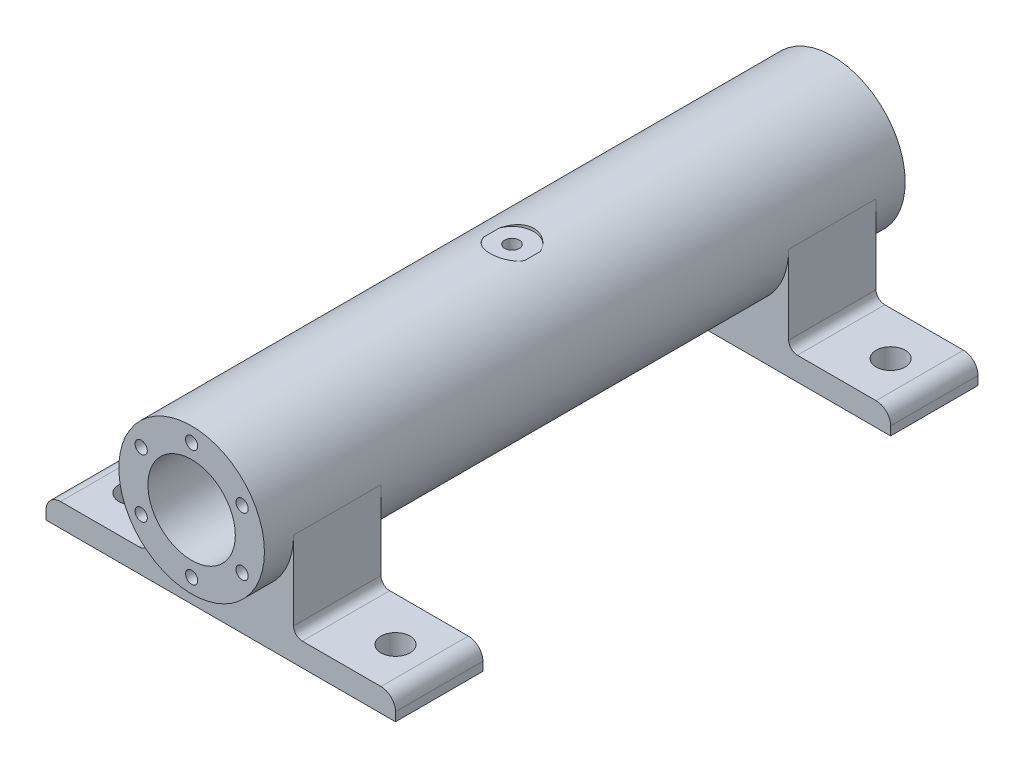
SolidWorks part; units mm, degrees
ref_plane "Front Plane" through (0, 0, 0) normal (0, 0, 1) x (1, 0, 0)
ref_plane "Top Plane" through (0, 0, 0) normal (0, 1, 0) x (1, 0, 0)
ref_plane "Right Plane" through (0, 0, 0) normal (1, 0, 0) x (0, 0, -1)
sketch "Sketch1" plane through (0, 0, 0) normal (0, 0, 1) x (1, 0, 0)
  circle A0 centre (0, 0) radius 25
  circle A1 centre (0, 0) radius 15
  dimension "D1" = 50
  dimension "D2" = 30
extrude "Boss-Extrude1" add sketch "Sketch1" along normal blind 220
hole_wizard "M5x0.8 Tapped Hole1" positions "Sketch3" profile "Sketch2" tap size "M5x0.8" standard "Ansi Metric"
sketch "Sketch3" plane through (0, 0, 220) normal (0, 0, 1) x (1, 0, 0)
  point P0 (0, 20)
  dimension "D1" = 0
  dimension "D2" = 20
sketch "Sketch2" plane through (0, 20, 220) normal (1, 0, 0) x (0, -1, 0)
  line L0 (0, 0) -> (0, 15.2618)
  line L1 (0, 15.2618) -> (2.1, 14)
  line L2 (2.1, 14) -> (2.1, 0)
  line L5 (2.1, 0) -> (0, 0)
  line L10 (0, 15.2618) -> (-2.1, 14) construction
  line L11 (0, -6.35) -> (0, 107.95) construction
  dimension "Tap Drill Dia." = 4.2
  dimension "Tap Drill Depth" = 14
  dimension "Drill Angle" = 118
cosmetic thread "Hole Thread1" parameters "D1"=10, "D2"=5
pattern_circular "CirPattern1" count 6 over 360 about axis through (0, 0, 0) along (0, 0, 1) of "M5x0.8 Tapped Hole1"
ref_plane "Plane1" through (0, 0, 110) normal (0, 0, 1) x (1, 0, 0)
mirror "Mirror1" about plane through (0, 0, 110) normal (0, 0, 1) of "CirPattern1", "M5x0.8 Tapped Hole1"
ref_plane "Plane2" through (0, 25, 0) normal (0, 1, 0) x (-1, 0, 0)
sketch "Sketch11" plane through (0, 25, 0) normal (0, 1, 0) x (-1, 0, 0)
  line L0 (27.5, 110) -> (-27.5, 110) construction
  circle A0 centre (0, 110) radius 7.5
  dimension "D1" = 15
extrude "Cut-Extrude2" cut sketch "Sketch11" against normal blind 1
sketch "Sketch13" plane through (0, 0, 0) normal (0, 1, 0) x (1, 0, 0)
  line L0 (-15, -220) -> (15, -220) construction
  line L1 (-60, -210) -> (60, -210)
  line L2 (-60, -210) -> (-60, -180)
  line L3 (-60, -180) -> (60, -180)
  line L4 (60, -210) -> (60, -180)
  line L5 (0, -220) -> (0, 0) construction
  dimension "D1" = 120
  dimension "D2" = 30
  dimension "D3" = 10
  dimension "D4" = 60
extrude "Boss-Extrude3" add sketch "Sketch13" against normal blind 38
mirror "Mirror2" about plane through (0, 0, 110) normal (0, 0, 1) of "Boss-Extrude3"
sketch "Sketch15" plane through (0, 0, 220) normal (0, 0, 1) x (1, 0, 0)
  circle A0 centre (0, 0) radius 15
  dimension "D1" = 30
extrude "Cut-Extrude3" cut sketch "Sketch15" against normal through all
sketch "Sketch16" plane through (0, 0, 210) normal (0, 0, 1) x (1, 0, 0)
  line L0 (-60, -30) -> (-25, -30)
  line L1 (-60, -38) -> (-60, 0) construction
  line L2 (-25, -30) -> (-25, 0)
  line L3 (-60, 0) -> (-25, 0) construction
  line L4 (-25, 0) -> (-60, 0)
  line L5 (-60, 0) -> (-60, -30)
  arc A0 (-25, 0) -> (25, 0) centre (0, 0) ccw construction
extrude "Cut-Extrude4" cut sketch "Sketch16" against normal blind 38
mirror "Mirror3" about plane through (0, 0, 0) normal (1, 0, 0) of "Cut-Extrude4"
mirror "Mirror4" about plane through (0, 0, 110) normal (0, 0, 1) of "Mirror3", "Cut-Extrude4"
fillet "Fillet1" radius 5 4 edges at (60, -30, 25) (-60, -30, 25) (60, -30, 195) (-60, -30, 195)
fillet "Fillet2" radius 3 4 edges at (-25, -30, 25) (25, -30, 25) (25, -30, 195) (-25, -30, 195)
hole_wizard "Ø10.0 (10) Diameter Hole1" positions "Sketch20" profile "Sketch19" hole size "Ø10.0" standard "ISO"
sketch "Sketch20" plane through (0, -30, 0) normal (0, 1, 0) x (-1, 0, 0)
  line L0 (55, 10) -> (28, 10) construction
  line L1 (60, 40) -> (60, 10) construction
  point P0 (45, 25)
  dimension "D1" = 15
  dimension "D2" = 15
sketch "Sketch19" plane through (-45, -30, 25) normal (1, 0, 0) x (0, 0, 1)
  line L0 (0, 0) -> (0, 14.0043)
  line L1 (0, 14.0043) -> (5, 11)
  line L2 (5, 11) -> (5, 0)
  line L5 (5, 0) -> (0, 0)
  line L10 (0, 14.0043) -> (-5, 11) construction
  line L11 (0, -6.35) -> (0, 107.95) construction
  dimension "Hole Dia." = 10
  dimension "Hole Depth" = 11
  dimension "Drill Angle" = 118
hole_wizard "M6x1.0 Tapped Hole1" positions "Sketch24" profile "Sketch25" tap size "M6x1.0" standard "Ansi Metric"
sketch "Sketch24" plane through (0, 24, 0) normal (0, 1, 0) x (-1, 0, 0)
  line L0 (0, 220) -> (0, 0) construction
  line L1 (34.65, 110) -> (-34.65, 110) construction
  point P0 (0, 110)
  dimension "D1" = 0
  dimension "D2" = 0
sketch "Sketch25" plane through (0, 24, 110) normal (1, 0, 0) x (0, 0, 1)
  line L0 (0, 0) -> (0, 18.5022)
  line L1 (0, 18.5022) -> (2.5, 17)
  line L2 (2.5, 17) -> (2.5, 0)
  line L5 (2.5, 0) -> (0, 0)
  line L10 (0, 18.5022) -> (-2.5, 17) construction
  line L11 (0, -6.35) -> (0, 107.95) construction
  dimension "Tap Drill Dia." = 5
  dimension "Tap Drill Depth" = 17
  dimension "Drill Angle" = 118
cosmetic thread "Hole Thread2" parameters "D1"=9.2098, "D2"=6
pattern_linear "LPattern1" count 2 spacing 90 along (1, 0, 0) count 2 spacing 170 along (0, 0, 1) of "Ø10.0 (10) Diameter Hole1"
